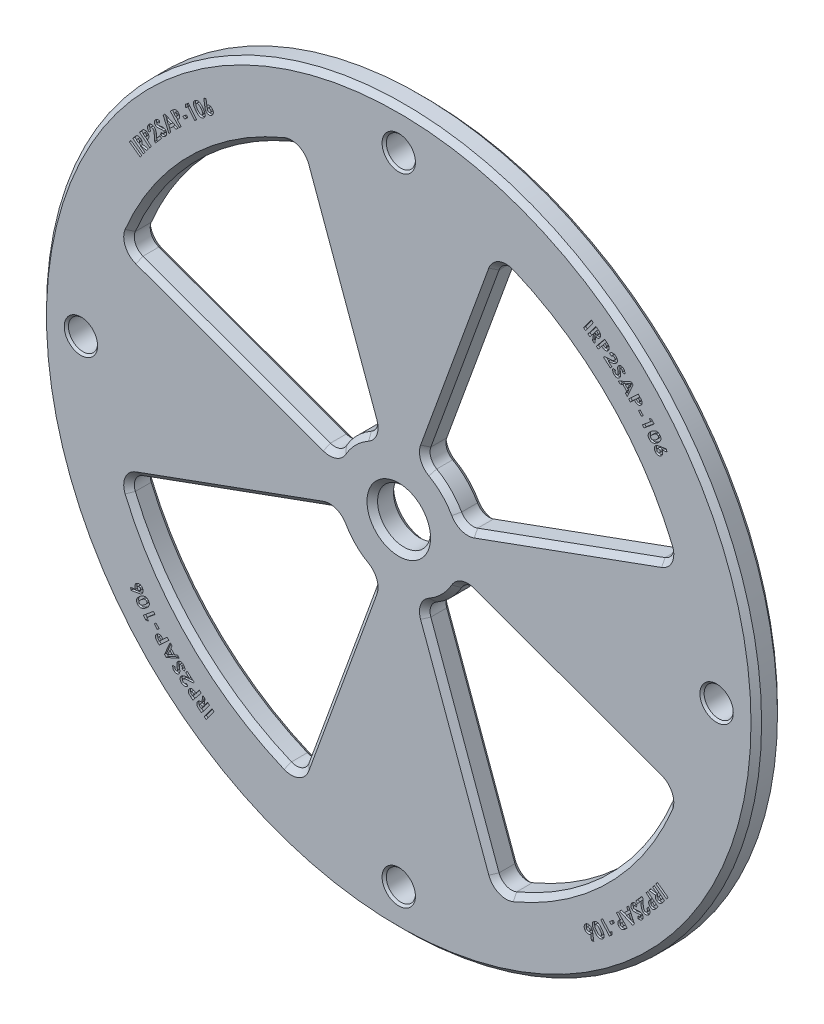
SolidWorks part; units mm, degrees
material "6061-T6 (SS)"
ref_plane "Front" through (0, 0, 0) normal (0, 0, 1) x (1, 0, 0)
ref_plane "Top" through (0, 0, 0) normal (0, 1, 0) x (1, 0, 0)
ref_plane "Right" through (0, 0, 0) normal (1, 0, 0) x (0, 0, -1)
sketch "Sketch1" plane through (0, 0, 0) normal (0, 0, 1) x (1, 0, 0)
  line L0 (-23.8901, 65.6375) -> (-5.4296, 14.9176)
  line L1 (-14.9176, 5.4296) -> (-65.6375, 23.8901)
  line L2 (65.6375, 23.8901) -> (14.9176, 5.4296)
  line L3 (5.4296, 14.9176) -> (23.8901, 65.6375)
  line L4 (23.8901, -65.6375) -> (5.4296, -14.9176)
  line L5 (14.9176, -5.4296) -> (65.6375, -23.8901)
  line L6 (-65.6375, -23.8901) -> (-14.9176, -5.4296)
  line L7 (-5.4296, -14.9176) -> (-23.8901, -65.6375)
  line L8 (0, 76.2) -> (0, 0) construction
  line L9 (0, 0) -> (-76.2, 0) construction
  circle A0 centre (0, 0) radius 85.725
  circle A1 centre (0, 0) radius 6.35
  circle A2 centre (0, 0) radius 76.2 construction
  circle A3 centre (0, 76.2) radius 3.4925
  circle A4 centre (76.2, 0) radius 3.4925
  circle A5 centre (0, -76.2) radius 3.4925
  circle A6 centre (-76.2, 0) radius 3.4925
  arc A7 (-65.6375, 23.8901) -> (-23.8901, 65.6375) centre (0, 0) cw
  arc A8 (-5.4296, 14.9176) -> (-14.9176, 5.4296) centre (0, 0) ccw
  arc A9 (23.8901, 65.6375) -> (65.6375, 23.8901) centre (0, 0) cw
  arc A10 (14.9176, 5.4296) -> (5.4296, 14.9176) centre (0, 0) ccw
  arc A11 (65.6375, -23.8901) -> (23.8901, -65.6375) centre (0, 0) cw
  arc A12 (5.4296, -14.9176) -> (14.9176, -5.4296) centre (0, 0) ccw
  arc A13 (-23.8901, -65.6375) -> (-65.6375, -23.8901) centre (0, 0) cw
  arc A14 (-14.9176, -5.4296) -> (-5.4296, -14.9176) centre (0, 0) ccw
  point P19 (-67.177, 15.6338)
  point P40 (0, 0)
  dimension "D1" = 6.985
  dimension "D2" = 152.4
  dimension "D3" = 171.45
  dimension "D4" = 12.7
  dimension "D8" = 69.85
  dimension "D9" = 15.875
  dimension "D6" = 20
  dimension "D7" = 20
  dimension "D5" = 4
extrude "Boss-Extrude1" add sketch "Sketch1" along normal blind 6.35
fillet "Fillet1" radius 3.175 16 edges at (5.4296, 14.9176, 3.175) (14.9176, 5.4296, 3.175) (14.9176, -5.4296, 3.175) (5.4296, -14.9176, 3.175) (-5.4296, -14.9176, 3.175) (-14.9176, -5.4296, 3.175) (-14.9176, 5.4296, 3.175) (-5.4296, 14.9176, 3.175) (-23.8901, 65.6375, 3.175) (23.8901, 65.6375, 3.175) (65.6375, 23.8901, 3.175) (65.6375, -23.8901, 3.175) (23.8901, -65.6375, 3.175) (-23.8901, -65.6375, 3.175) (-65.6375, -23.8901, 3.175) (-65.6375, 23.8901, 3.175)
chamfer "Chamfer1" distance 1.27 angle 45 68 edges at (6.35, 0, 0) (6.35, 0, 6.35) (14.6013, 40.1168, 0) (6.4282, 15.4684, 0) (24.4889, 64.4057, 0) (11.2253, 11.2253, 0) (49.3914, 49.3914, 0) (15.4684, 6.4282, 0) (64.4057, 24.4889, 0) (40.1168, 14.6013, 0) (14.6013, 40.1168, 6.35) (6.4282, 15.4684, 6.35) (24.4889, 64.4057, 6.35) (11.2253, 11.2253, 6.35) (49.3914, 49.3914, 6.35) (15.4684, 6.4282, 6.35) (64.4057, 24.4889, 6.35) (40.1168, 14.6013, 6.35) (40.1168, -14.6013, 0) (15.4684, -6.4282, 0) (64.4057, -24.4889, 0) (11.2253, -11.2253, 0) (49.3914, -49.3914, 0) (6.4282, -15.4684, 0) (24.4889, -64.4057, 0) (14.6013, -40.1168, 0) (40.1168, -14.6013, 6.35) (15.4684, -6.4282, 6.35) (64.4057, -24.4889, 6.35) (11.2253, -11.2253, 6.35) (49.3914, -49.3914, 6.35) (6.4282, -15.4684, 6.35) (24.4889, -64.4057, 6.35) (14.6013, -40.1168, 6.35) (-14.6013, -40.1168, 0) (-6.4282, -15.4684, 0) (-24.4889, -64.4057, 0) (-11.2253, -11.2253, 0) (-49.3914, -49.3914, 0) (-15.4684, -6.4282, 0) (-64.4057, -24.4889, 0) (-40.1168, -14.6013, 0) (-14.6013, 40.1168, 0) (-24.4889, 64.4057, 0) (-6.4282, 15.4684, 0) (-49.3914, 49.3914, 0) (-11.2253, 11.2253, 0) (-64.4057, 24.4889, 0) (-15.4684, 6.4282, 0) (-40.1168, 14.6013, 0) (-14.6013, -40.1168, 6.35) (-6.4282, -15.4684, 6.35) (-24.4889, -64.4057, 6.35) (-11.2253, -11.2253, 6.35) (-49.3914, -49.3914, 6.35) (-15.4684, -6.4282, 6.35) (-64.4057, -24.4889, 6.35) (-40.1168, -14.6013, 6.35) (-14.6013, 40.1168, 6.35) (-24.4889, 64.4057, 6.35) (-6.4282, 15.4684, 6.35) (-49.3914, 49.3914, 6.35) (-11.2253, 11.2253, 6.35) (-64.4057, 24.4889, 6.35) (-15.4684, 6.4282, 6.35) (-40.1168, 14.6013, 6.35) (85.725, 0, 0) (85.725, 0, 6.35)
chamfer "Chamfer2" distance 0.508 angle 45 8 edges at (3.4925, -76.2, 0) (3.4925, -76.2, 6.35) (79.6925, 0, 0) (79.6925, 0, 6.35) (3.4925, 76.2, 0) (3.4925, 76.2, 6.35) (-72.7075, 0, 0) (-72.7075, 0, 6.35)
sketch "Sketch2" plane through (0, 0, 6.35) normal (0, 0, 1) x (1, 0, 0)
  line L0 (0, 76.2) -> (0, 0) construction
  line L1 (0, 0) -> (76.2, 0) construction
  arc A1 (0, 76.2) -> (76.2, 0) centre (0, 0) cw construction
  circle A2 centre (0, 0) radius 7.62 construction
  arc A3 (76.2, 0) -> (0, -76.2) centre (0, 0) cw construction
  arc A4 (0, -76.2) -> (-76.2, 0) centre (0, 0) cw construction
  arc A5 (-76.2, 0) -> (0, 76.2) centre (0, 0) cw construction
  text T0 "<b>IRP2SAP-106</b>"
  text T1 "<b>IRP2SAP-106</b>\r\n"
  text T2 "<b>IRP2SAP-106</b>\r\n"
  text T3 "<b>IRP2SAP-106</b>"
  point P16 (0, 0)
  dimension "D1" = 76.2
  dimension "D2" = 4
extrude "Cut-Extrude1" cut sketch "Sketch2" against normal blind 0.508
